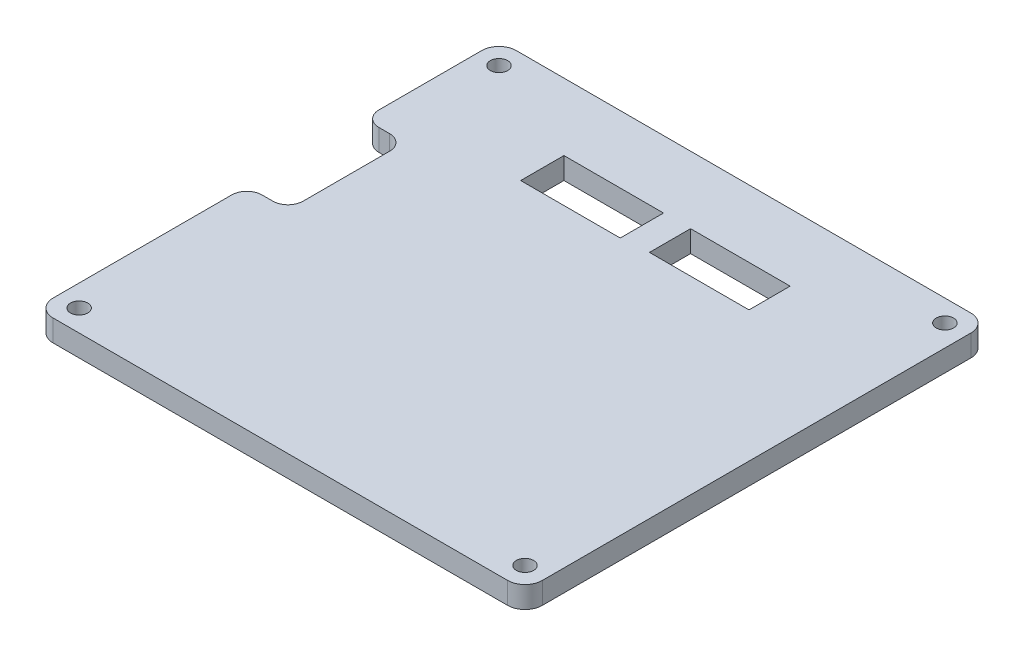
SolidWorks part; units mm, degrees
ref_plane "Front Plane" through (0, 0, 0) normal (0, 0, 1) x (1, 0, 0)
ref_plane "Top Plane" through (0, 0, 0) normal (0, 1, 0) x (1, 0, 0)
ref_plane "Right Plane" through (0, 0, 0) normal (1, 0, 0) x (0, 0, -1)
sketch "Sketch1" plane through (0, 0, 0) normal (0, 1, 0) x (1, 0, 0)
  line L1 (-56.5, -53.5) -> (56.5, -53.5)
  line L2 (-56.5, -53.5) -> (-56.5, 53.5)
  line L3 (-56.5, 53.5) -> (56.5, 53.5)
  line L4 (56.5, -53.5) -> (56.5, 53.5)
  line L5 (-56.5, -53.5) -> (56.5, 53.5) construction
  line L6 (-56.5, 53.5) -> (56.5, -53.5) construction
  point P0 (0, 0)
  dimension "D1" = 113
  dimension "D2" = 107
extrude "Main Body Back Plate" add sketch "Sketch1" along normal blind 5
ref_plane "Plane1" through (0, 0, 0) normal (-1, 0, 0) x (0, 0, 1)
sketch "Sketch3" plane through (0, 0, 0) normal (-1, 0, 0) x (0, 0, 1)
  line L0 (53.5, 0) -> (-53.5, -24.5849) construction
  line L1 (-53.5, -24.5849) -> (-53.5, 0) construction
  line L2 (-53.5, 0) -> (53.5, 0) construction
  line L4 (53.5, 5) -> (53.5, 0) construction
  line L5 (-53.5, 0) -> (53.5, 0) construction
  line L10 (33.5, 0) -> (33.5, -4.5953)
  line L11 (33.5, -4.5953) -> (53.5, 0)
  line L12 (53.5, 0) -> (33.5, 0)
  dimension "D1" = 12.94
  dimension "D3" = 20
extrude "Height Adjust" add sketch "Sketch3" along normal mid plane 40
sketch "Sketch4" plane through (0, 5, 0) normal (0, 1, 0) x (1, 0, 0)
  line L0 (-56.5, 53.5) -> (-56.5, -53.5) construction
  line L1 (-26, 28) -> (-3, 28)
  line L2 (-26, 28) -> (-26, 38)
  line L3 (-26, 38) -> (-3, 38)
  line L4 (-3, 28) -> (-3, 38)
  line L5 (-26, 28) -> (-3, 38) construction
  line L6 (-26, 38) -> (-3, 28) construction
  line L7 (3.25, 28.5) -> (26.25, 28.5)
  line L8 (3.25, 28.5) -> (3.25, 38)
  line L9 (3.25, 38) -> (26.25, 38)
  line L10 (26.25, 28.5) -> (26.25, 38)
  line L11 (3.25, 28.5) -> (26.25, 38) construction
  line L12 (3.25, 38) -> (26.25, 28.5) construction
  line L13 (56.5, 53.5) -> (-56.5, 53.5) construction
  line L14 (-14.5, 33) -> (14.75, 33.25) construction
  line L15 (0.125, 53.5) -> (0.125, 33.125) construction
  point P0 (-14.5, 33)
  point P5 (14.75, 33.25)
  dimension "D1" = 23
  dimension "D2" = 23
  dimension "D3" = 30.5
  dimension "D4" = 59.75
  dimension "D5" = 10
  dimension "D6" = 9.5
  dimension "D7" = 15.5
extrude "Hole Postitions" cut sketch "Sketch4" against normal blind 40
sketch "Sketch5" plane through (0, 5, 0) normal (0, 1, 0) x (1, 0, 0)
  line L0 (-56.5, -53.5) -> (56.5, -53.5) construction
  line L2 (-56.5, 53.5) -> (-56.5, -53.5) construction
  line L3 (56.5, -53.5) -> (56.5, 53.5) construction
  line L4 (56.5, 53.5) -> (-56.5, 53.5) construction
  circle A0 centre (-51.5, 48.5) radius 2
  circle A1 centre (-51.5, -48.5) radius 2
  circle A2 centre (51.5, -48.5) radius 2
  circle A3 centre (51.5, 48.5) radius 2
  dimension "D1" = 4
  dimension "D2" = 4
  dimension "D3" = 4
  dimension "D4" = 4
  dimension "D5" = 5
  dimension "D6" = 5
  dimension "D7" = 5
  dimension "D8" = 5
  dimension "D9" = 5
  dimension "D10" = 5
  dimension "D11" = 5
  dimension "D12" = 5
extrude "Screw Holes" cut sketch "Sketch5" against normal through all
fillet "Fillet1" radius 4 4 edges at (56.5, 2.5, -53.5) (56.5, 2.5, 53.5) (-56.5, 2.5, 53.5) (-56.5, 2.5, -53.5)
sketch "Sketch6" plane through (0, 0, 0) normal (0, -1, 0) x (1, 0, 0)
  line L0 (-56.5, -49.5) -> (-56.5, 49.5) construction
  line L1 (-47, 4.75) -> (-56.5, 4.75)
  line L2 (-47, 4.75) -> (-47, -22.25)
  line L3 (-47, -22.25) -> (-56.5, -22.25)
  line L4 (-56.5, 4.75) -> (-56.5, -22.25)
  line L5 (-47, 4.75) -> (-56.5, -22.25) construction
  line L6 (-47, -22.25) -> (-56.5, 4.75) construction
  line L7 (52.5, -53.5) -> (-52.5, -53.5) construction
  point P0 (-51.75, -8.75)
  dimension "D1" = 9.5
  dimension "D2" = 27
  dimension "D3" = 31.25
extrude "Cut-Extrude1" cut sketch "Sketch6" against normal blind 10
fillet "Fillet2" radius 3.5 4 edges at (-56.5, 2.5, 4.75) (-56.5, 2.5, -22.25) (-47, 2.5, 4.75) (-47, 2.5, -22.25)
